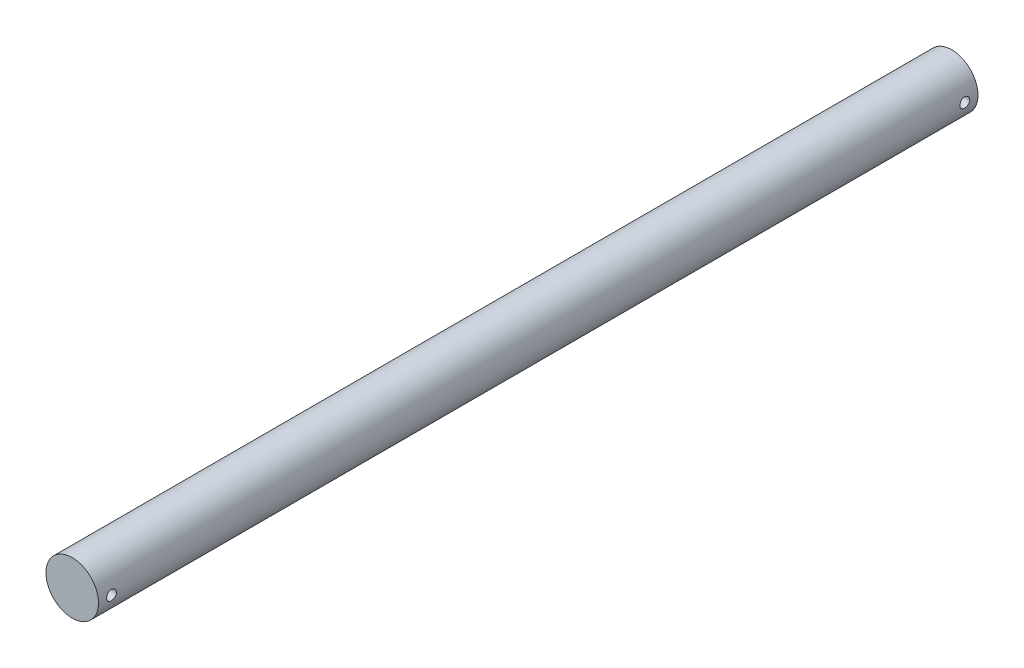
SolidWorks part; units mm, degrees
ref_plane "Front" through (0, 0, 0) normal (0, 0, 1) x (1, 0, 0)
ref_plane "Top" through (0, 0, 0) normal (0, 1, 0) x (1, 0, 0)
ref_plane "Right" through (0, 0, 0) normal (1, 0, 0) x (0, 0, -1)
sketch "Sketch2" plane through (0, 0, 0) normal (0, 0, 1) x (1, 0, 0)
  circle A0 centre (0, 0) radius 3.175
  dimension "D1" = 6.35
extrude "Boss-Extrude1" add sketch "Sketch2" along normal blind 50
sketch "Sketch3" plane through (0, 0, 50) normal (0, 0, 1) x (1, 0, 0)
  circle A0 centre (0, 0) radius 3.175
  circle A1 centre (0, 0) radius 3.175 construction
extrude "Boss-Extrude2" add sketch "Sketch3" along normal blind 3.175
sketch "Sketch4" plane through (0, 0, 53.175) normal (0, 0, 1) x (1, 0, 0)
  circle A0 centre (0, 0) radius 3.175
  dimension "D1" = 6.35
mirror "Mirror1" about plane through (0, 0, 0) normal (0, 0, 1) of "Boss-Extrude2", "Boss-Extrude1"
sketch "Sketch5" plane through (0, 0, 0) normal (1, 0, 0) x (0, 0, -1)
  line L1 (-53.175, 0) -> (53.175, 0) construction
  line L2 (-53.175, 3.175) -> (-53.175, -3.175) construction
  line L3 (53.175, -3.175) -> (53.175, 3.175) construction
  circle A0 centre (-51.5875, 0) radius 0.5953
  circle A1 centre (51.5875, 0) radius 0.5953
  point P2 (52.0667, 0)
  point P11 (-51.8427, 0)
  dimension "D2" = 1.1906
  dimension "D4" = 1.1906
  dimension "D1" = 1.5875
  dimension "D3" = 1.5875
extrude "Cut-Extrude1" cut sketch "Sketch5" against normal through all both and the other way through all
